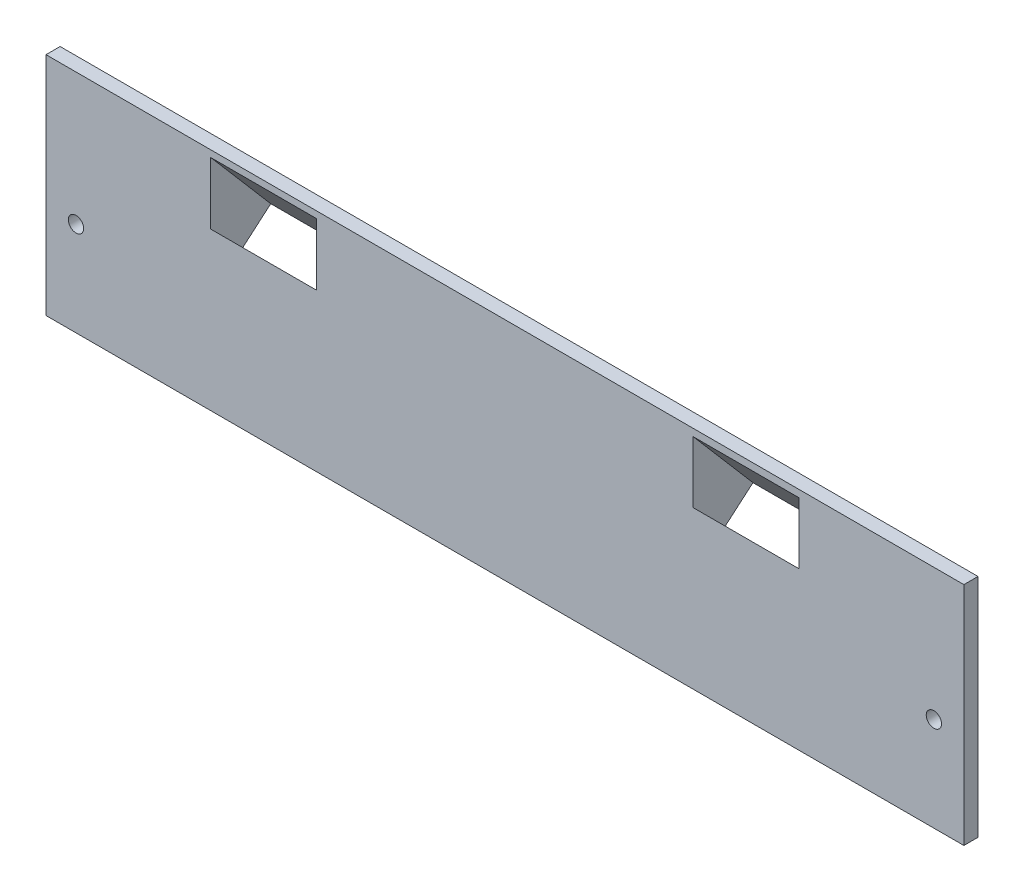
SolidWorks part; units mm, degrees
ref_plane "Alzado" through (0, 0, 0) normal (0, 0, 1) x (1, 0, 0)
ref_plane "Planta" through (0, 0, 0) normal (0, 1, 0) x (1, 0, 0)
ref_plane "Vista lateral" through (0, 0, 0) normal (1, 0, 0) x (0, 0, -1)
sketch "Croquis1" plane through (0, 0, 0) normal (0, 0, 1) x (1, 0, 0)
  line L0 (-97.5, 0) -> (97.5, 0)
  line L1 (97.5, 0) -> (97.5, 38)
  line L2 (97.5, 38) -> (-97.5, 38)
  line L3 (0, 0) -> (0, 28.0598) construction
  line L4 (-97.5, 0) -> (-97.5, 38)
  circle A2 centre (91.125, 15) radius 1.625
  circle A3 centre (-91.125, 15) radius 1.625
  point P13 (0, 38)
  point P14 (0, 0)
  dimension "D1" = 3.25
  dimension "D2" = 15
  dimension "D3" = 97.5
  dimension "D4" = 38
  dimension "D5" = 6.375
extrude "Saliente-Extruir1" add sketch "Croquis1" along normal blind 3
sketch "Croquis8" plane through (0, 0, 0) normal (0, -1, 0) x (1, 0, 0)
  line L1 (-97.5, 3) -> (97.5, 3)
  line L2 (-97.5, 3) -> (-97.5, 0)
  line L3 (-97.5, 0) -> (97.5, 0)
  line L4 (97.5, 3) -> (97.5, 0)
extrude "Saliente-Extruir5" add sketch "Croquis8" along normal blind 5
sketch "Croquis9" plane through (0, 38, 0) normal (0, 1, 0) x (1, 0, 0)
  line L1 (-97.5, 0) -> (97.5, 0)
  line L2 (-97.5, 0) -> (-97.5, -3)
  line L3 (-97.5, -3) -> (97.5, -3)
  line L4 (97.5, 0) -> (97.5, -3)
extrude "Saliente-Extruir6" add sketch "Croquis9" along normal blind 5
sketch "Croquis10" plane through (97.5, 0, 0) normal (1, 0, 0) x (0, 0, -1)
  line L0 (0, 39.4998) -> (11.1006, 26.5486)
  line L1 (1.23, 18.0885) -> (0, 17.0343)
  line L2 (0, 39.4998) -> (0, 17.0343)
  line L3 (0, -5) -> (0, 43) construction
  line L4 (11.1006, 26.5486) -> (1.23, 18.0885)
  line L6 (-3, 23.0238) -> (0, 19.5236) construction
  line L7 (-3, -5) -> (-3, 43) construction
  line L8 (-3, 23.0238) -> (5.5756, 30.374) construction
  dimension "D2" = 6.5
extrude "Saliente-Extruir7" add sketch "Croquis10" against normal blind 35 from offset 25 offset against normal yes
sketch "Croquis11" plane through (0, 9.8201, 8.4169) normal (0, -0.7593, -0.6508) x (1, 0, 0)
  line L0 (37.5, -11.0855) -> (37.5, -25.7055) construction
  line L3 (62.5, -16.2055) -> (40, -16.2055)
  line L6 (40, -16.2055) -> (40, -24.7055)
  line L7 (40, -24.7055) -> (62.5, -24.7055)
  line L8 (62.5, -24.7055) -> (62.5, -16.2055)
  line L10 (37.5, -25.7055) -> (72.5, -25.7055) construction
  dimension "D1" = 8.5
  dimension "D2" = 22.5
  dimension "D3" = 2.5
  dimension "D4" = 1
extrude "Cortar-Extruir4" cut sketch "Croquis11" against normal through all both and the other way through all
sketch "Croquis12" plane through (72.5, 0, 0) normal (1, 0, 0) x (0, 0, -1)
  line L0 (11.1006, 26.5486) -> (0, 17.0343)
  line L1 (0, 17.0343) -> (0, 23.6195)
  line L2 (0, -5) -> (0, 43) construction
  line L3 (0, 23.6195) -> (7.8467, 30.345)
  line L4 (11.1006, 26.5486) -> (0, 39.4998) construction
  line L5 (7.8467, 30.345) -> (11.1006, 26.5486)
  dimension "D1" = 5
extrude "Cortar-Extruir5" cut sketch "Croquis12" against normal up to next
sketch "Croquis13" plane through (0, 13.6165, 11.6707) normal (0, -0.7593, -0.6508) x (1, 0, 0)
  line L1 (62.5, -24.7055) -> (40, -24.7055) construction
  line L2 (72.5, -25.7055) -> (72.5, -15.371) construction
  circle A0 centre (66.25, -20.2055) radius 1
  dimension "D1" = 2
  dimension "D2" = 6.25
  dimension "D3" = 4.5
extrude "Cortar-Extruir6" cut sketch "Croquis13" against normal blind 5
sketch "Croquis14" plane through (-97.5, 0, 0) normal (-1, 0, 0) x (0, 0, 1)
  line L0 (0, 23.6195) -> (-7.8467, 30.345)
  line L1 (-7.8467, 30.345) -> (0, 39.4998)
  line L2 (0, 39.4998) -> (0, 23.6195)
extrude "Saliente-Extruir8" add sketch "Croquis14" against normal blind 35 from offset 25 offset against normal yes
sketch "Croquis16" plane through (0, 13.6165, 11.6707) normal (0, -0.7593, -0.6508) x (1, 0, 0)
  line L0 (0, 0) -> (0, -29.2293) construction
  line L5 (-40, -24.7778) -> (-62.5, -24.7778)
  line L6 (-62.5, -16.2055) -> (-62.5, -24.7778)
  line L7 (-40, -16.2055) -> (-40, -24.7778)
  line L8 (-40, -16.2055) -> (-62.5, -16.2055)
  line L15 (-37.5, -25.7055) -> (-37.5, -15.371) construction
  dimension "D1" = 2.5
extrude "Cortar-Extruir7" cut sketch "Croquis16" against normal through all both and the other way through all
sketch "Croquis17" plane through (0, 13.6165, 11.6707) normal (0, -0.7593, -0.6508) x (1, 0, 0)
  line L0 (0, 0) -> (0, -24) construction
  line L3 (-62.5, -16.2055) -> (-62.5, -24.7778) construction
  circle A1 centre (-66.25, -20.2055) radius 1
  dimension "D1" = 3.75
extrude "Cortar-Extruir8" cut sketch "Croquis17" against normal blind 5
sketch "Croquis18" plane through (0, 13.6165, 11.6707) normal (0, -0.7593, -0.6508) x (1, 0, 0)
  line L0 (-72.5, -25.7055) -> (-37.5, -25.7055)
  line L1 (-62.5, -16.2055) -> (-40, -16.2055)
  line L2 (-62.5, -16.2055) -> (-62.5, -24.7778)
  line L3 (-62.5, -24.7778) -> (-40, -24.7778)
  line L4 (-40, -16.2055) -> (-40, -24.7778)
  line L5 (40, -16.2055) -> (62.5, -16.2055)
  line L6 (40, -16.2055) -> (40, -24.7055)
  line L7 (40, -24.7055) -> (62.5, -24.7055)
  line L8 (62.5, -16.2055) -> (62.5, -24.7055)
  line L9 (-37.5, -25.7055) -> (-37.5, -13.7055)
  line L10 (-37.5, -13.7055) -> (-72.5, -13.7055)
  line L11 (-72.5, -13.7055) -> (-72.5, -25.7055)
  line L12 (37.5, -25.7055) -> (72.5, -25.7055)
  line L13 (72.5, -25.7055) -> (72.5, -13.7055)
  line L14 (72.5, -13.7055) -> (37.5, -13.7055)
  line L15 (37.5, -13.7055) -> (37.5, -25.7055)
  circle A0 centre (-66.25, -20.2055) radius 1
  circle A1 centre (66.25, -20.2055) radius 1
  dimension "D1" = 2.5
extrude "Saliente-Extruir9" add sketch "Croquis18" against normal up to surface (4.9736 mm away) from offset 4
